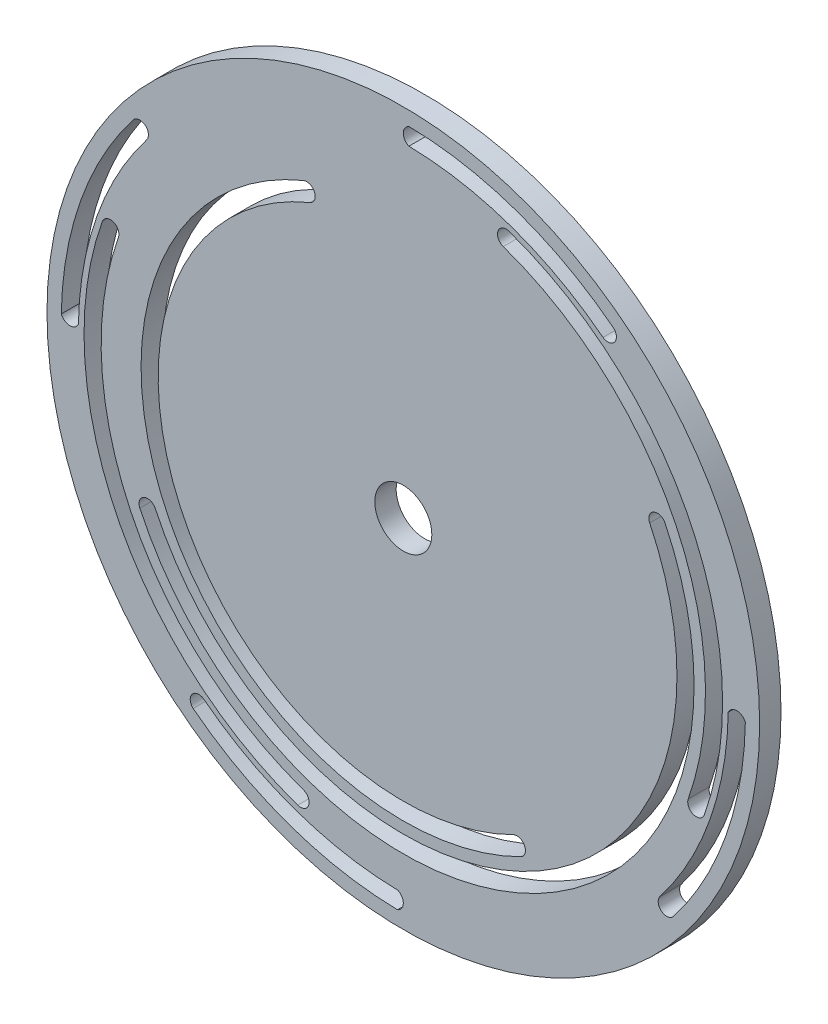
SolidWorks part; units mm, degrees
ref_plane "Alzado" through (0, 0, 0) normal (0, 0, 1) x (1, 0, 0)
ref_plane "Planta" through (0, 0, 0) normal (0, 1, 0) x (1, 0, 0)
ref_plane "Vista lateral" through (0, 0, 0) normal (1, 0, 0) x (0, 0, -1)
sketch "Croquis1" plane through (0, 0, 0) normal (0, 0, 1) x (1, 0, 0)
  circle A0 centre (0, 0) radius 50
  arc A3 (0.7808, 45.5933) -> (0.8219, 47.993) centre (1.2992, 46.7846) cw
  arc A4 (29.4928, 37.8705) -> (28.0182, 35.9769) centre (28.6992, 36.9676) cw
  arc A5 (29.4928, 37.8705) -> (0.8219, 47.993) centre (0, 0) ccw
  arc A6 (28.0182, 35.9769) -> (0.7808, 45.5933) centre (0, 0) ccw
  arc A7 (35.9769, -28.0182) -> (45.5933, -0.7808) centre (0, 0) ccw
  arc A8 (37.8705, -29.4928) -> (47.993, -0.8219) centre (0, 0) ccw
  arc A9 (37.8705, -29.4928) -> (35.9769, -28.0182) centre (36.9676, -28.6992) cw
  arc A10 (45.5933, -0.7808) -> (47.993, -0.8219) centre (46.7846, -1.2992) cw
  arc A11 (-28.0182, -35.9769) -> (-0.7808, -45.5933) centre (0, 0) ccw
  arc A12 (-29.4928, -37.8705) -> (-0.8219, -47.993) centre (0, 0) ccw
  arc A13 (-29.4928, -37.8705) -> (-28.0182, -35.9769) centre (-28.6992, -36.9676) cw
  arc A14 (-0.7808, -45.5933) -> (-0.8219, -47.993) centre (-1.2992, -46.7846) cw
  arc A15 (-35.9769, 28.0182) -> (-45.5933, 0.7808) centre (0, 0) ccw
  arc A16 (-37.8705, 29.4928) -> (-47.993, 0.8219) centre (0, 0) ccw
  arc A17 (-37.8705, 29.4928) -> (-35.9769, 28.0182) centre (-36.9676, 28.6992) cw
  arc A18 (-45.5933, 0.7808) -> (-47.993, 0.8219) centre (-46.7846, 1.2992) cw
  arc A19 (42.2389, -14.9304) -> (14.817, 42.2788) centre (0, 0) ccw
  arc A20 (39.9761, -14.1306) -> (14.0233, 40.0139) centre (0, 0) ccw
  arc A21 (14.817, 42.2788) -> (14.0233, 40.0139) centre (14.4201, 41.1463) ccw
  arc A22 (42.2389, -14.9304) -> (39.9761, -14.1306) centre (41.1075, -14.5305) cw
  arc A23 (-39.9761, 14.1306) -> (-14.0233, -40.0139) centre (0, 0) ccw
  arc A24 (-14.817, -42.2788) -> (-14.0233, -40.0139) centre (-14.4201, -41.1463) ccw
  arc A25 (-42.2389, 14.9304) -> (-14.817, -42.2788) centre (0, 0) ccw
  arc A26 (-42.2389, 14.9304) -> (-39.9761, 14.1306) centre (-41.1075, 14.5305) cw
  arc A27 (-36.9676, -17.2638) -> (36.7337, 17.756) centre (0, 0) ccw
  arc A28 (-34.793, -16.2483) -> (34.5729, 16.7116) centre (0, 0) ccw
  arc A29 (36.7337, 17.756) -> (34.5729, 16.7116) centre (35.6533, 17.2338) ccw
  arc A30 (-36.9676, -17.2638) -> (-34.793, -16.2483) centre (-35.8803, -16.7561) cw
  arc A31 (-14.0233, 34.0233) -> (16.4803, -32.9035) centre (0, 0) ccw
  arc A32 (-13.1087, 31.8044) -> (15.4055, -30.7576) centre (0, 0) ccw
  arc A33 (16.4803, -32.9035) -> (15.4055, -30.7576) centre (15.9429, -31.8306) ccw
  arc A34 (-14.0233, 34.0233) -> (-13.1087, 31.8044) centre (-13.566, 32.9139) cw
  circle A35 centre (0, 0) radius 4
  point P34 (0, 0)
  point P47 (0, 0)
  dimension "D1" = 4
  dimension "D2" = 2
extrude "Saliente-Extruir3" add sketch "Croquis1" along normal blind 3 contours A34 A31 A33 A32 | A18 A15 A17 A16 | A30 A27 A29 A28 | A14 A11 A13 A12 | A10 A7 A9 A8 | A22 A19 A21 A20 | A6 A4 A5 A3 | A35 | A0 | A23 A24 A25 A26
